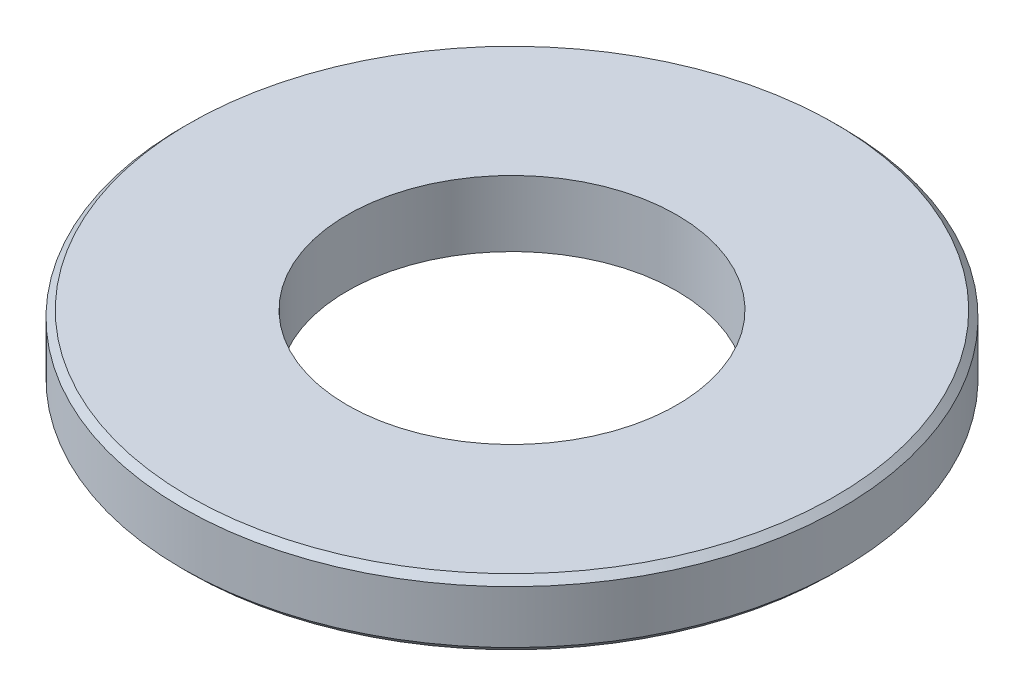
SolidWorks part; units mm, degrees
material "6061-T6 (SS)"
ref_plane "Front Plane" through (0, 0, 0) normal (0, 0, 1) x (1, 0, 0)
ref_plane "Top Plane" through (0, 0, 0) normal (0, 1, 0) x (1, 0, 0)
ref_plane "Right Plane" through (0, 0, 0) normal (1, 0, 0) x (0, 0, -1)
sketch "Sketch1" plane through (0, 0, 0) normal (0, 1, 0) x (1, 0, 0)
  circle A0 centre (0, 0) radius 12.7
  circle A1 centre (0, 0) radius 6.35
  dimension "D1" = 25.4
  dimension "D2" = 12.7
extrude "Boss-Extrude1" add sketch "Sketch1" along normal blind 2.54
chamfer "Chamfer1" distance 0.254 angle 45 2 edges at (0, 0, 12.7) (0, 2.54, 12.7)
